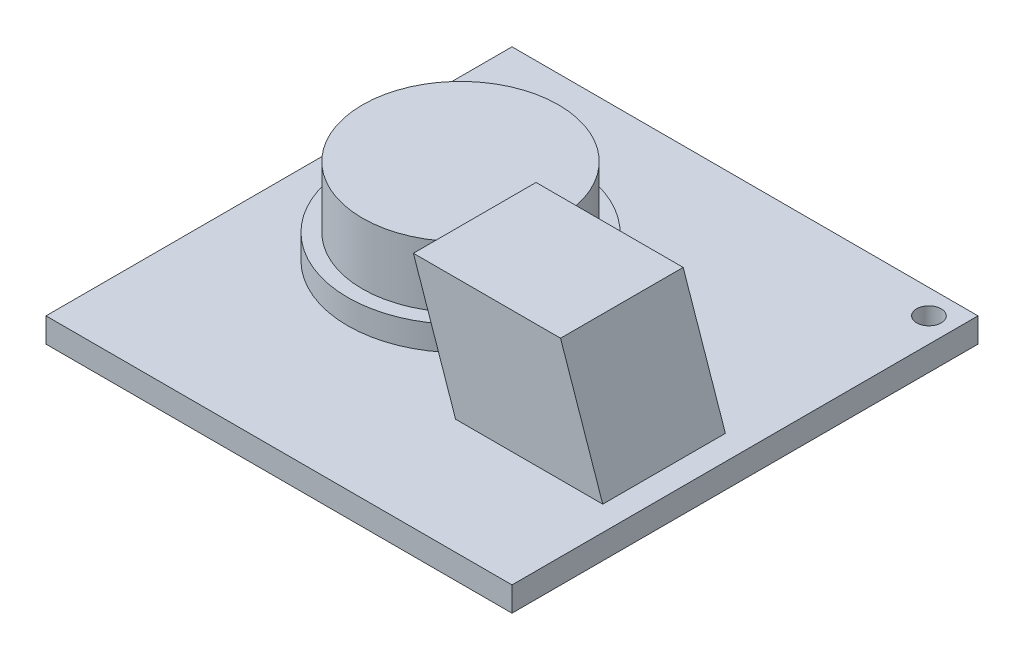
SolidWorks part; units mm, degrees
ref_plane "Спереди" through (0, 0, 0) normal (0, 0, 1) x (1, 0, 0)
ref_plane "Сверху" through (0, 0, 0) normal (0, 1, 0) x (1, 0, 0)
ref_plane "Справа" through (0, 0, 0) normal (1, 0, 0) x (0, 0, -1)
sketch "Эскиз1" plane through (0, 0, 0) normal (0, 1, 0) x (1, 0, 0)
  line L1 (-36.0691, -7.5072) -> (-17.0691, -7.5072)
  line L2 (-36.0691, -7.5072) -> (-36.0691, -26.5072)
  line L3 (-36.0691, -26.5072) -> (-17.0691, -26.5072)
  line L4 (-17.0691, -7.5072) -> (-17.0691, -26.5072)
extrude "Бобышка-Вытянуть1" add sketch "Эскиз1" along normal blind 1
sketch "Эскиз2" plane through (0, 1, 0) normal (0, 1, 0) x (1, 0, 0)
  line L1 (-17.0691, -7.5072) -> (-18.0691, -7.5072) construction
  line L2 (-17.0691, -7.5072) -> (-17.0691, -8.5072) construction
  line L3 (-17.0691, -8.5072) -> (-18.0691, -8.5072) construction
  line L4 (-18.0691, -7.5072) -> (-18.0691, -8.5072) construction
  circle A0 centre (-18.0691, -8.5072) radius 0.5
extrude "Вырез-Вытянуть1" cut sketch "Эскиз2" against normal blind 1 contours A0
sketch "Эскиз3" plane through (0, 1, 0) normal (0, 1, 0) x (1, 0, 0)
  circle A0 centre (-29.5691, -16.1072) radius 4.6
extrude "Бобышка-Вытянуть2" add sketch "Эскиз3" along normal blind 1 contours A0
sketch "Эскиз5" plane through (0, 2, 0) normal (0, 1, 0) x (1, 0, 0)
  circle A0 centre (-29.5691, -16.1072) radius 4
extrude "Бобышка-Вытянуть3" add sketch "Эскиз5" along normal blind 2.5 contours A0
sketch "Эскиз6" plane through (0, 1, 0) normal (0, 1, 0) x (1, 0, 0)
  line L1 (-24.0691, -16.8072) -> (-18.0691, -16.8072)
  line L2 (-24.0691, -16.8072) -> (-24.0691, -21.8072)
  line L3 (-24.0691, -21.8072) -> (-18.0691, -21.8072)
  line L4 (-18.0691, -16.8072) -> (-18.0691, -21.8072)
sketch "Эскиз9" plane through (0, 0, 0) normal (0, 0, 1) x (1, 0, 0)
  line L0 (-24.0691, 1) -> (-25.7896, 6)
  line L2 (-24.0691, 1) -> (-24.0691, 6) construction
  line L3 (-24.2096, 6) -> (-27.3008, 6) construction
  line L4 (-36.0691, 1) -> (-17.0691, 1) construction
sweep "По траектории1" add profiles "Эскиз6" path "Эскиз9"
